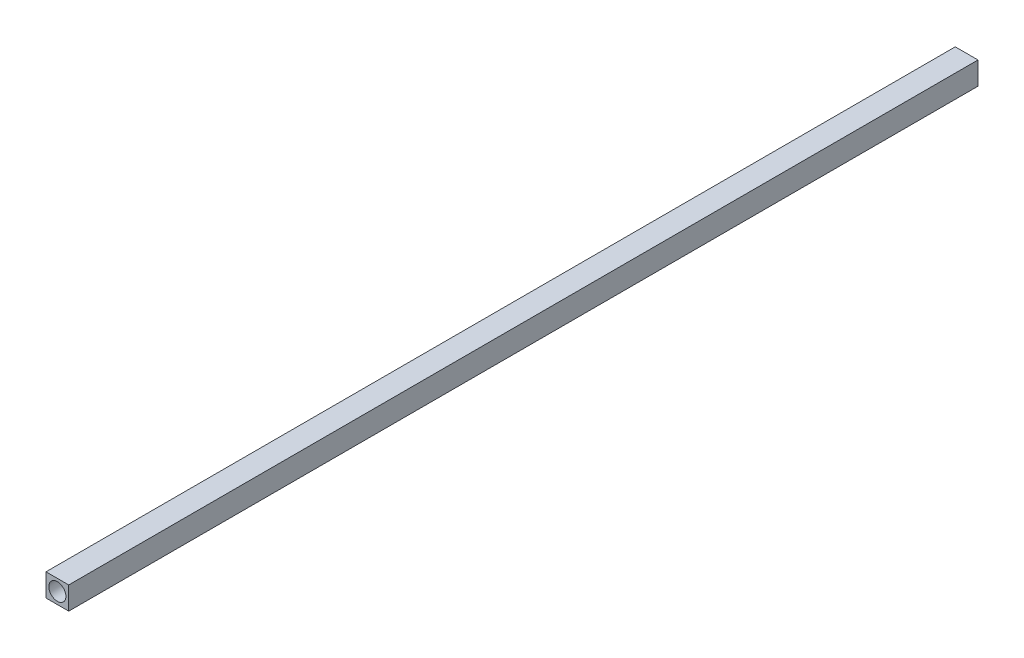
SolidWorks part; units mm, degrees
ref_plane "Front Plane" through (0, 0, 0) normal (0, 0, 1) x (1, 0, 0)
ref_plane "Top Plane" through (0, 0, 0) normal (0, 1, 0) x (1, 0, 0)
ref_plane "Right Plane" through (0, 0, 0) normal (1, 0, 0) x (0, 0, -1)
sketch "Sketch1" plane through (0, 0, 0) normal (0, 0, 1) x (1, 0, 0)
  line L0 (2, 4) -> (2, 0) construction
  line L1 (0, 0) -> (4, 0)
  line L2 (0, 0) -> (0, 4)
  line L3 (0, 4) -> (4, 4)
  line L4 (4, 0) -> (4, 4)
  line L5 (0, 2) -> (4, 2) construction
  circle A0 centre (2, 2) radius 1.5
  dimension "D3" = 3
  dimension "D1" = 4
  dimension "D2" = 4
extrude "Boss-Extrude1" add sketch "Sketch1" along normal blind 160
